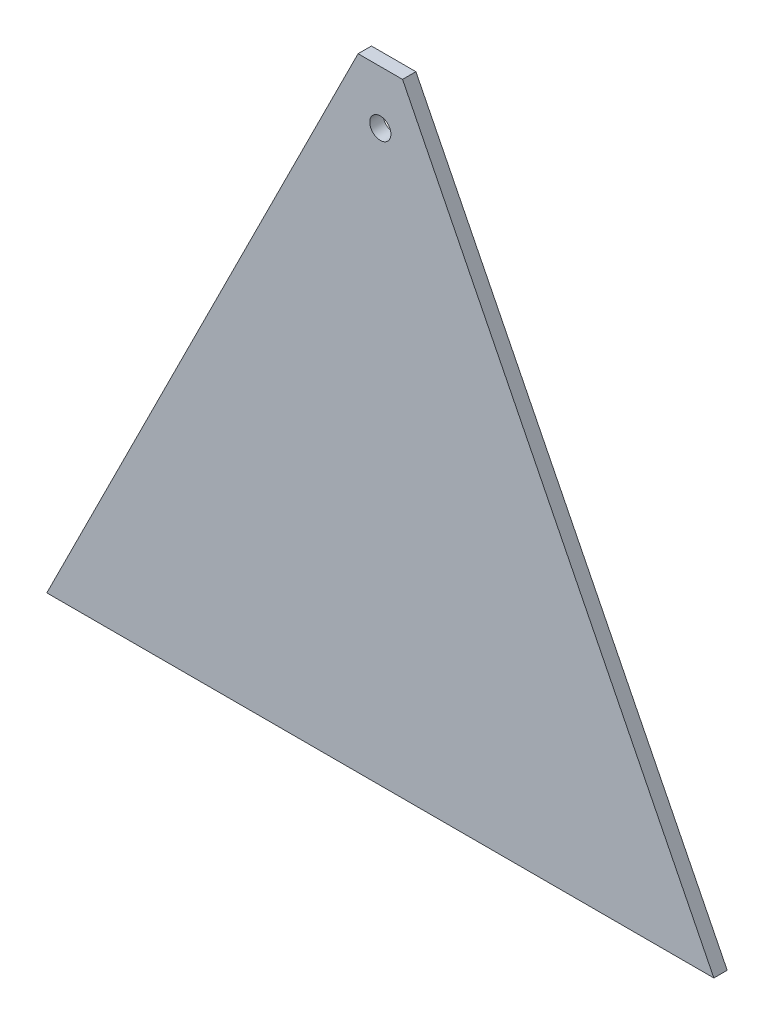
SolidWorks part; units mm, degrees
material "Balsa"
ref_plane "Alzado" through (0, 0, 0) normal (0, 0, 1) x (1, 0, 0)
ref_plane "Planta" through (0, 0, 0) normal (0, 1, 0) x (1, 0, 0)
ref_plane "Vista lateral" through (0, 0, 0) normal (1, 0, 0) x (0, 0, -1)
sketch "Croquis1" plane through (0, 0, 0) normal (0, 0, 1) x (1, 0, 0)
  line L0 (0, 150) -> (0, -176.1405) construction
  line L1 (-146.095, 0) -> (168.9269, 0) construction
  line L2 (75, 0) -> (-75, 0)
  line L3 (-75, 0) -> (0, 150)
  line L4 (75, 0) -> (0, 150)
  point P9 (0, 0)
  dimension "D1" = 75
  dimension "D2" = 150
extrude "Saliente-Extruir1" add sketch "Croquis1" along normal blind 3
sketch "Croquis2" plane through (0, 0, 0) normal (0, 0, 1) x (1, 0, 0)
  line L0 (-34.6969, 128) -> (31.6762, 128) construction
  line L1 (0, -14.0881) -> (0, 160.498) construction
  line L2 (75, 0) -> (0, 150) construction
  line L3 (0, 150) -> (-75, 0) construction
  line L4 (5, 140) -> (0, 150)
  line L5 (0, 150) -> (-5, 140)
  line L6 (-5, 140) -> (5, 140)
  circle A0 centre (0, 128) radius 2.3812
  dimension "D3" = 4.7625
  dimension "D1" = 10
  dimension "D2" = 12
extrude "Cortar-Extruir1" cut sketch "Croquis2" along normal through all
